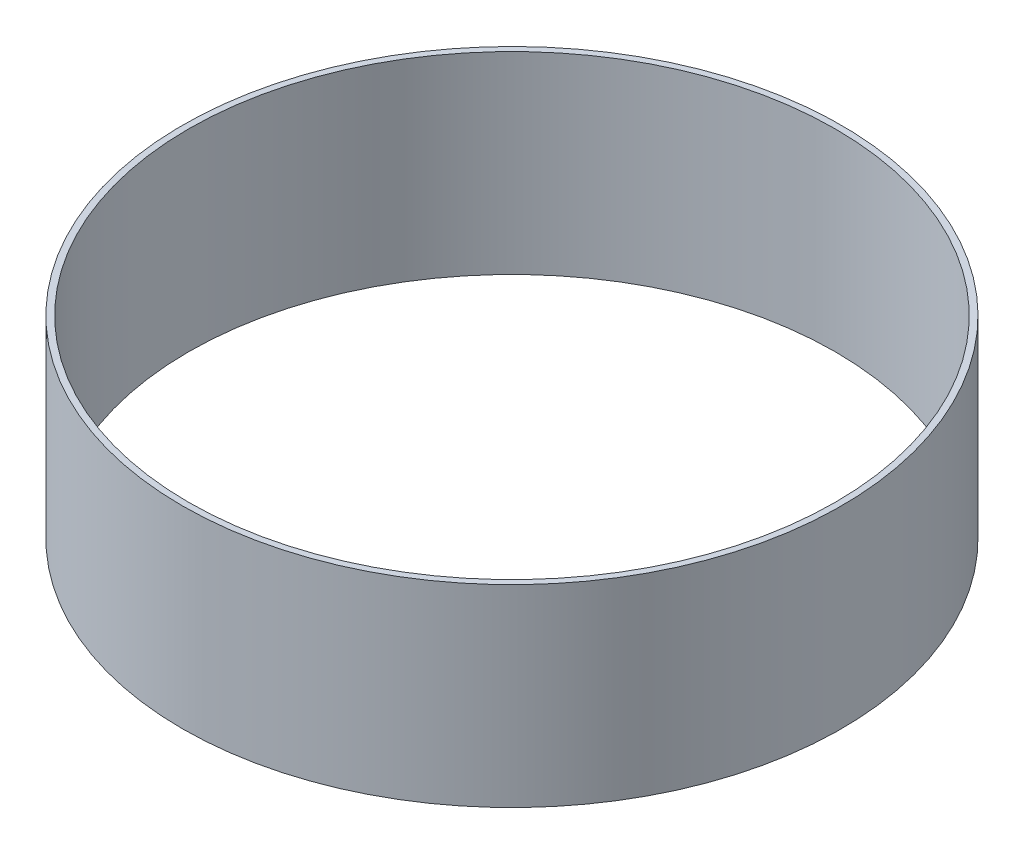
SolidWorks part; units mm, degrees
material "75mm-CastingTube"
ref_plane "Front Plane" through (0, 0, 0) normal (0, 0, 1) x (1, 0, 0)
ref_plane "Top Plane" through (0, 0, 0) normal (0, 1, 0) x (1, 0, 0)
ref_plane "Right Plane" through (0, 0, 0) normal (1, 0, 0) x (0, 0, -1)
sketch "Sketch1" plane through (0, 0, 0) normal (0, 1, 0) x (1, 0, 0)
  circle A0 centre (0, 0) radius 32.4612
  circle A1 centre (0, 0) radius 33.0835
  dimension "D1" = 64.9224
  dimension "D2" = 66.167
extrude "Boss-Extrude1" add sketch "Sketch1" along normal blind 19.3802
